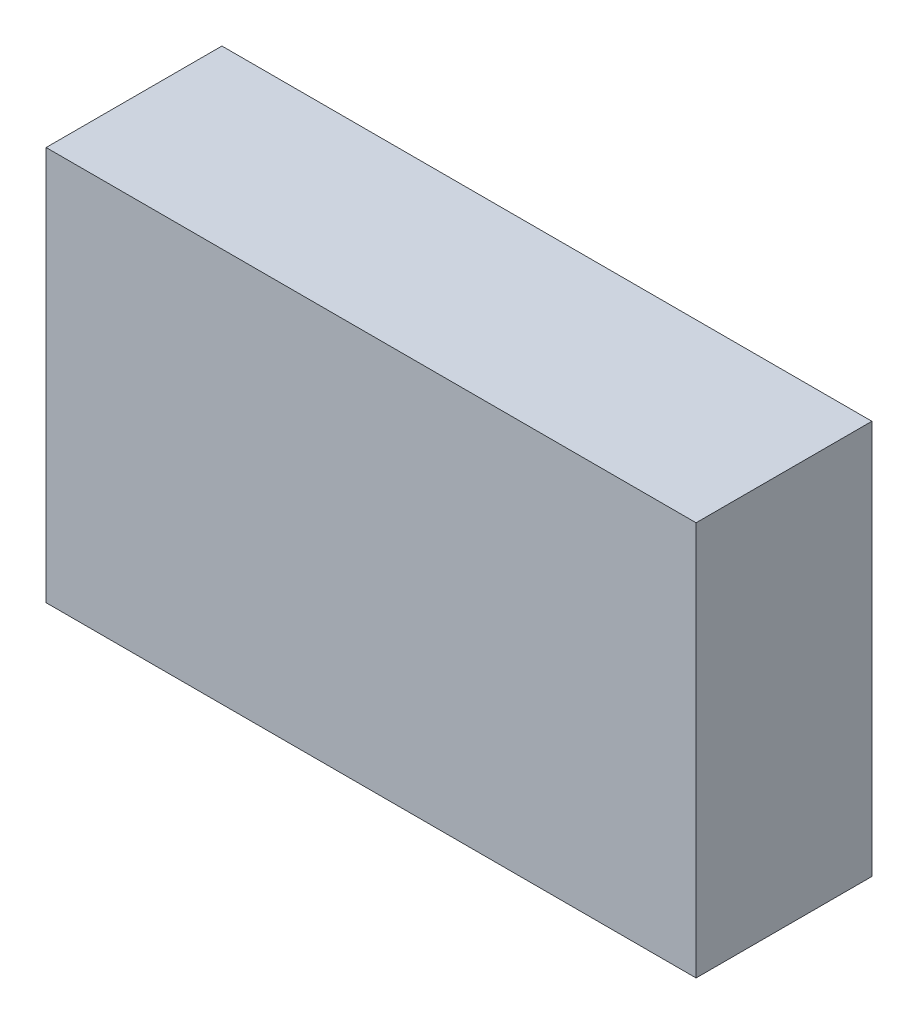
SolidWorks part; units mm, degrees
ref_plane "Front Plane" through (0, 0, 0) normal (0, 0, 1) x (1, 0, 0)
ref_plane "Top Plane" through (0, 0, 0) normal (0, 1, 0) x (1, 0, 0)
ref_plane "Right Plane" through (0, 0, 0) normal (1, 0, 0) x (0, 0, -1)
sketch "Sketch1" plane through (0, 0, 0) normal (0, 0, 1) x (1, 0, 0)
  line L1 (-154.94, 93.98) -> (154.94, 93.98)
  line L2 (-154.94, 93.98) -> (-154.94, -93.98)
  line L3 (-154.94, -93.98) -> (154.94, -93.98)
  line L4 (154.94, 93.98) -> (154.94, -93.98)
  line L5 (-154.94, 93.98) -> (154.94, -93.98) construction
  line L6 (-154.94, -93.98) -> (154.94, 93.98) construction
  point P0 (0, 0)
  dimension "D1" = 309.88
  dimension "D2" = 187.96
extrude "Boss-Extrude1" add sketch "Sketch1" along normal blind 83.82
